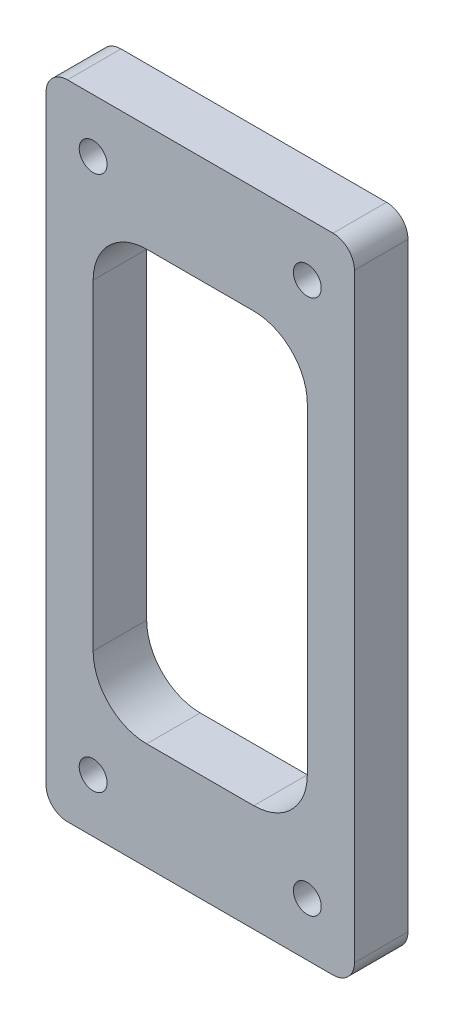
SolidWorks part; units mm, degrees
material "PLA"
ref_plane "Blat stołu" through (0, 0, 0) normal (0, 0, 1) x (1, 0, 0)
ref_plane "Płaszczyzna górna" through (0, 0, 0) normal (0, 1, 0) x (1, 0, 0)
ref_plane "Płaszczyzna prawa" through (0, 0, 0) normal (1, 0, 0) x (0, 0, -1)
sketch "Szkic1" plane through (0, 0, 0) normal (0, 0, 1) x (1, 0, 0)
  line L1 (-14.4, 30) -> (14.4, 30)
  line L2 (-14.4, 30) -> (-14.4, -30)
  line L3 (-14.4, -30) -> (14.4, -30)
  line L4 (14.4, 30) -> (14.4, -30)
  line L5 (-14.4, 30) -> (14.4, -30) construction
  line L6 (-14.4, -30) -> (14.4, 30) construction
  point P0 (0, 0)
  dimension "D1" = 28.8
  dimension "D2" = 60
extrude "Dodanie-wyciągnięcie1" add sketch "Szkic1" along normal blind 5
sketch "Szkic2" plane through (0, 0, 5) normal (0, 0, 1) x (1, 0, 0)
  line L5 (-10, -25) -> (10, -25)
  line L6 (-10, -25) -> (-10, 25)
  line L7 (-10, 25) -> (10, 25)
  line L8 (10, -25) -> (10, 25)
  line L9 (-10, -25) -> (10, 25) construction
  line L10 (-10, 25) -> (10, -25) construction
  point P0 (0, 0)
  dimension "D2" = 50
  dimension "D1" = 20
fillet "Zaokrąglenie1" radius 2 4 edges at (-14.4, 30, 2.5) (-14.4, -30, 2.5) (14.4, -30, 2.5) (14.4, 30, 2.5)
hole_wizard "Otwór pod śrubę M22" positions "Szkic5" profile "Szkic6" hole size "M2" standard "ISO" end condition through all
sketch "Szkic5" plane through (0, 0, 5) normal (0, 0, 1) x (1, 0, 0)
  point P0 (10, 25)
  point P3 (10, -25)
  point P6 (-10, -25)
  point P9 (-10, 25)
sketch "Szkic6" plane through (10, 25, 5) normal (1, 0, 0) x (0, -1, 0)
  line L0 (0, 0) -> (0, 5)
  line L1 (0, 5) -> (1.3, 5)
  line L2 (1.3, 5) -> (1.3, 0)
  line L5 (1.3, 0) -> (0, 0)
  line L11 (0, -6.35) -> (0, 107.95) construction
  dimension "Średnica otworu na wylot" = 2.6
  dimension "Głębokość otworu na wylot" = 5
sketch "Szkic7" plane through (0, 0, 5) normal (0, 0, 1) x (1, 0, 0)
  line L1 (5, 20) -> (-5, 20)
  line L2 (10, 15) -> (10, -15)
  line L3 (5, -20) -> (-5, -20)
  line L4 (-10, 15) -> (-10, -15)
  line L5 (10, 20) -> (-10, -20) construction
  line L6 (10, -20) -> (-10, 20) construction
  arc A0 (5, 20) -> (10, 15) centre (5, 15) cw
  arc A1 (-10, 15) -> (-5, 20) centre (-5, 15) cw
  arc A2 (10, -15) -> (5, -20) centre (5, -15) cw
  arc A3 (-10, -15) -> (-5, -20) centre (-5, -15) ccw
  point P0 (0, 0)
  dimension "D3" = 5
  dimension "D4" = 5
  dimension "D5" = 5
  dimension "D6" = 5
  dimension "D1" = 40
  dimension "D2" = 20
extrude "Wytnij-wyciągnięcie1" cut sketch "Szkic7" against normal up to next
